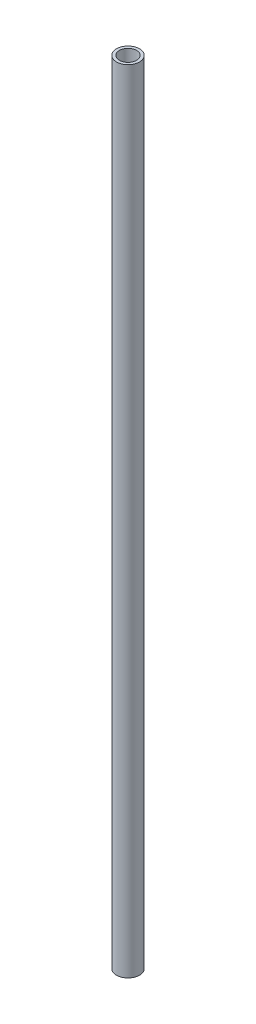
SolidWorks part; units mm, degrees
material "AISI Type 316L stainless steel"
ref_plane "Front Plane" through (0, 0, 0) normal (0, 0, 1) x (1, 0, 0)
ref_plane "Top Plane" through (0, 0, 0) normal (0, 1, 0) x (1, 0, 0)
ref_plane "Right Plane" through (0, 0, 0) normal (1, 0, 0) x (0, 0, -1)
sketch "Sketch1" plane through (0, 0, 0) normal (0, 1, 0) x (1, 0, 0)
  circle A0 centre (0, 0) radius 12.7
  circle A1 centre (0, 0) radius 9.525
  dimension "D1" = 19.05
  dimension "D2" = 25.4
extrude "Boss-Extrude1" add sketch "Sketch1" along normal mid plane 876.3
